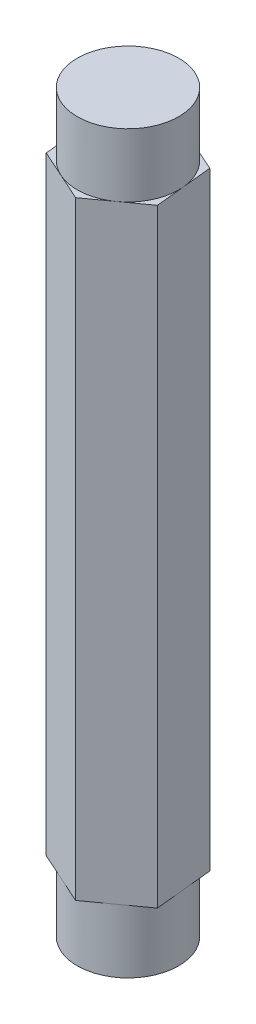
SolidWorks part; units mm, degrees
ref_plane "Front Plane" through (0, 0, 0) normal (0, 0, 1) x (1, 0, 0)
ref_plane "Top Plane" through (0, 0, 0) normal (0, 1, 0) x (1, 0, 0)
ref_plane "Right Plane" through (0, 0, 0) normal (1, 0, 0) x (0, 0, -1)
sketch "Sketch1" plane through (0, 0, 0) normal (0, 1, 0) x (1, 0, 0)
  line L1 (5.9488, 4.2866) -> (-0.7379, 7.2951)
  line L2 (-0.7379, 7.2951) -> (-6.6867, 3.0085)
  line L3 (-6.6867, 3.0085) -> (-5.9488, -4.2866)
  line L4 (-5.9488, -4.2866) -> (0.7379, -7.2951)
  line L5 (0.7379, -7.2951) -> (6.6867, -3.0085)
  line L6 (6.6867, -3.0085) -> (5.9488, 4.2866)
  circle A0 centre (0, 0) radius 6.35 construction
extrude "Boss-Extrude1" add sketch "Sketch1" along normal blind 76.2
sketch "Sketch3" plane through (0, 0, 0) normal (0, -1, 0) x (-1, 0, 0)
  circle A0 centre (0, 0) radius 6.35
extrude "Boss-Extrude2" add sketch "Sketch3" along normal blind 7.9375
sketch "Sketch4" plane through (0, 76.2, 0) normal (0, 1, 0) x (1, 0, 0)
  circle A0 centre (0, 0) radius 6.35
extrude "Boss-Extrude3" add sketch "Sketch4" along normal blind 7.9375 contours A0
